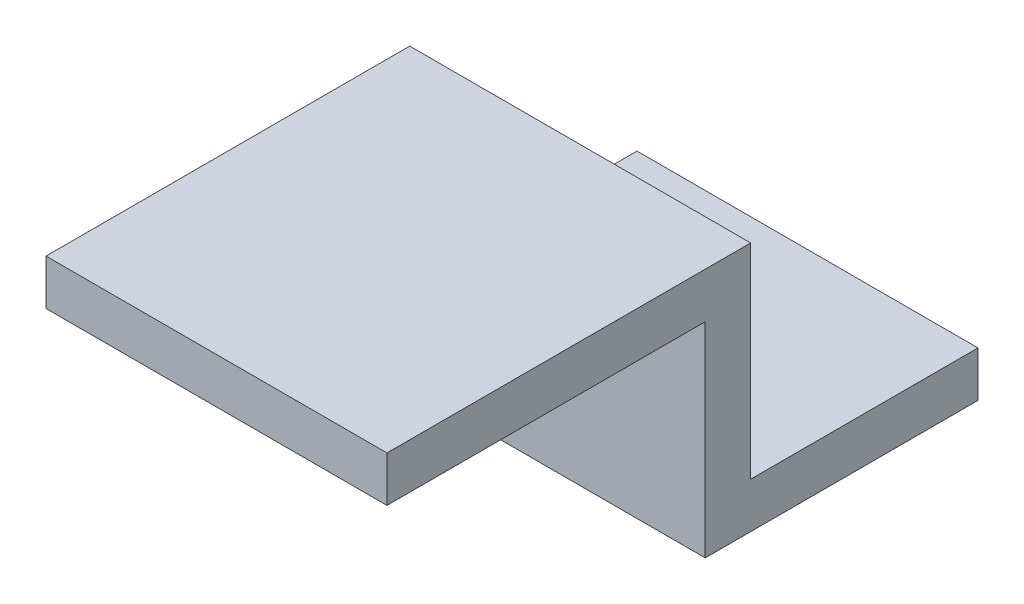
SolidWorks part; units mm, degrees
ref_plane "Front Plane" through (0, 0, 0) normal (0, 0, 1) x (1, 0, 0)
ref_plane "Top Plane" through (0, 0, 0) normal (0, 1, 0) x (1, 0, 0)
ref_plane "Right Plane" through (0, 0, 0) normal (1, 0, 0) x (0, 0, -1)
sketch "Sketch1" plane through (0, 0, 0) normal (1, 0, 0) x (0, 0, -1)
  line L0 (0, 0) -> (16, 0)
  line L1 (16, 0) -> (16, -9)
  line L2 (16, -9) -> (26, -9)
  line L3 (26, -9) -> (26, -11)
  line L4 (26, -11) -> (14, -11)
  line L5 (14, -11) -> (14, -2)
  line L6 (14, -2) -> (0, -2)
  line L7 (0, -2) -> (0, 0)
  dimension "D1" = 2
  dimension "D2" = 16
  dimension "D3" = 14
  dimension "D4" = 9
  dimension "D5" = 9
  dimension "D6" = 2
  dimension "D7" = 12
  dimension "D8" = 11
  dimension "D9" = 2
extrude "Boss-Extrude1" add sketch "Sketch1" against normal blind 15
sketch "Sketch3" plane through (0, -9, 0) normal (0, 1, 0) x (1, 0, 0)
  line L0 (-7.5, 26) -> (-7.5, 16) construction
  line L1 (-15, 26) -> (0, 26) construction
  line L2 (-15, 16) -> (0, 16) construction
  line L3 (0, 21) -> (-15, 21) construction
  line L4 (0, 26) -> (0, 16) construction
  line L5 (-15, 26) -> (-15, 16) construction
  circle A0 centre (-7.5, 21) radius 1.5
  dimension "D1" = 3
  dimension "D2" = 5
  dimension "D3" = 7.5
extrude "Cut-Extrude1" cut sketch "Sketch3" against normal up to next
